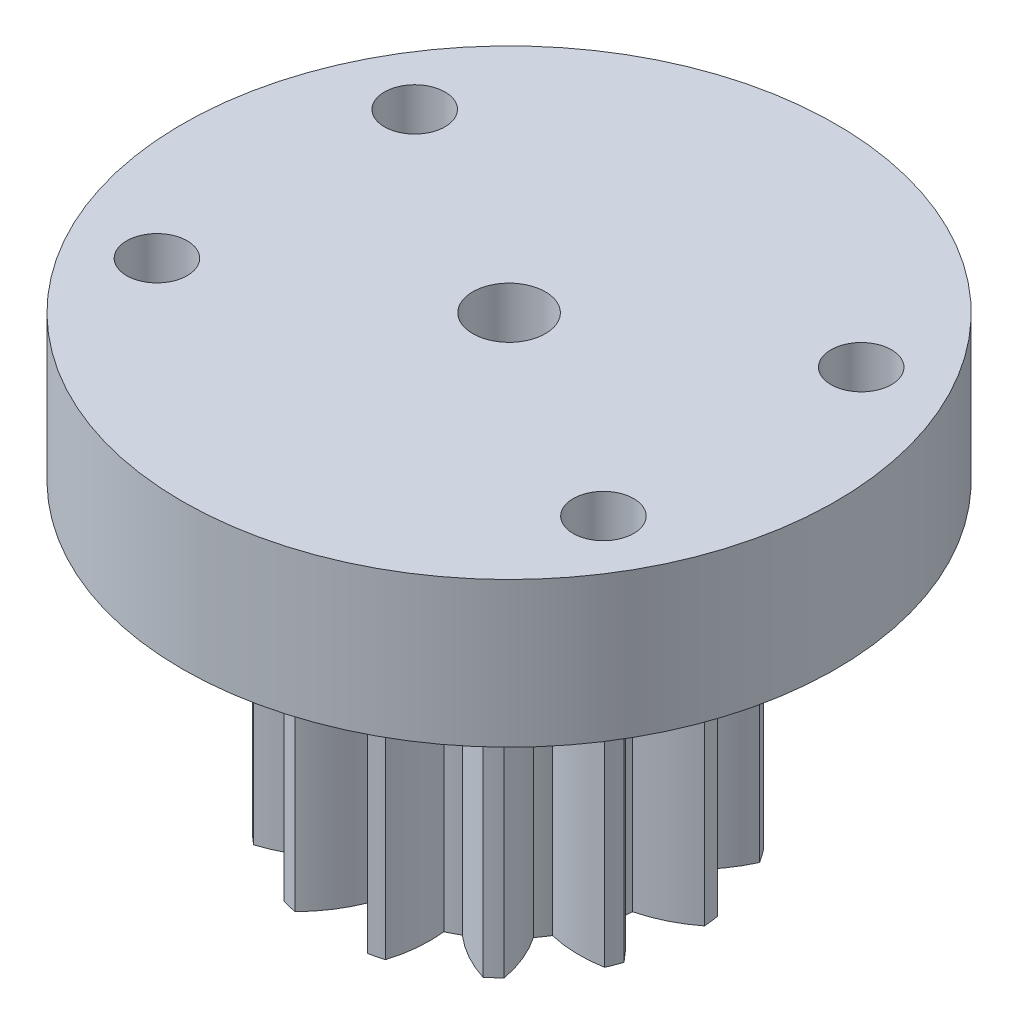
SolidWorks part; units mm, degrees
material "PLA"
ref_plane "Front Plane" through (0, 0, 0) normal (0, 0, 1) x (1, 0, 0)
ref_plane "Top Plane" through (0, 0, 0) normal (0, 1, 0) x (1, 0, 0)
ref_plane "Right Plane" through (0, 0, 0) normal (1, 0, 0) x (0, 0, -1)
sketch "Sketch1" plane through (0, 0, 0) normal (0, 1, 0) x (1, 0, 0)
  line L0 (0, 0) -> (0, 10.3828) construction
  arc A0 (0.31, 7.4936) -> (-0.31, 7.4936) centre (0, 0) ccw
  circle A1 centre (0, 0) radius 5.5
  arc A2 (-1.04, 5.4008) -> (-0.31, 7.4936) centre (4.3152, 4.7065) cw
  arc A3 (1.04, 5.4008) -> (0.31, 7.4936) centre (-4.3152, 4.7065) ccw
  arc A4 (1.589, 5.2655) -> (3.208, 6.7793) centre (6.0081, 2.1621) cw
  arc A5 (3.4307, 4.2988) -> (3.7569, 6.4912) centre (-1.6337, 6.1728) ccw
  arc A6 (3.7569, 6.4912) -> (3.208, 6.7793) centre (0, 0) ccw
  arc A7 (3.854, 3.9239) -> (5.991, 4.512) centre (6.3247, -0.8777) cw
  arc A8 (5.0355, 2.2121) -> (6.3432, 4.0017) centre (1.4221, 6.225) ccw
  arc A9 (6.3432, 4.0017) -> (5.991, 4.512) centre (0, 0) ccw
  arc A10 (5.236, 1.6834) -> (7.4016, 1.211) centre (5.1924, -3.7164) cw
  arc A11 (5.4868, -0.3814) -> (7.4763, 0.5955) centre (4.1521, 4.851) ccw
  arc A12 (7.4763, 0.5955) -> (7.4016, 1.211) centre (0, 0) ccw
  arc A13 (5.4186, -0.9427) -> (7.1166, -2.3674) centre (2.8705, -5.7037) cw
  arc A14 (4.681, -2.8876) -> (6.8967, -2.9471) centre (5.9309, 2.3658) ccw
  arc A15 (6.8967, -2.9471) -> (7.1166, -2.3674) centre (0, 0) ccw
  arc A16 (4.3598, -3.3529) -> (5.2012, -5.4035) centre (-0.1089, -6.3844) cw
  arc A17 (2.8029, -4.7322) -> (4.7371, -5.8146) centre (6.351, -0.6614) ccw
  arc A18 (4.7371, -5.8146) -> (5.2012, -5.4035) centre (0, 0) ccw
  arc A19 (2.3023, -4.995) -> (2.0943, -7.2017) centre (-3.0634, -5.6025) cw
  arc A20 (0.2827, -5.4927) -> (1.4923, -7.35) centre (5.3161, -3.5371) ccw
  arc A21 (1.4923, -7.35) -> (2.0943, -7.2017) centre (0, 0) ccw
  arc A22 (-0.2827, -5.4927) -> (-1.4923, -7.35) centre (-5.3161, -3.5371) cw
  arc A23 (-2.3023, -4.995) -> (-2.0943, -7.2017) centre (3.0634, -5.6025) ccw
  arc A24 (-2.0943, -7.2017) -> (-1.4923, -7.35) centre (0, 0) ccw
  arc A25 (-2.8029, -4.7322) -> (-4.7371, -5.8146) centre (-6.351, -0.6614) cw
  arc A26 (-4.3598, -3.3529) -> (-5.2012, -5.4035) centre (0.1089, -6.3844) ccw
  arc A27 (-5.2012, -5.4035) -> (-4.7371, -5.8146) centre (0, 0) ccw
  arc A28 (-4.681, -2.8876) -> (-6.8967, -2.9471) centre (-5.9309, 2.3658) cw
  arc A29 (-5.4186, -0.9427) -> (-7.1166, -2.3674) centre (-2.8705, -5.7037) ccw
  arc A30 (-7.1166, -2.3674) -> (-6.8967, -2.9471) centre (0, 0) ccw
  arc A31 (-5.4868, -0.3814) -> (-7.4763, 0.5955) centre (-4.1521, 4.851) cw
  arc A32 (-5.236, 1.6834) -> (-7.4016, 1.211) centre (-5.1924, -3.7164) ccw
  arc A33 (-7.4016, 1.211) -> (-7.4763, 0.5955) centre (0, 0) ccw
  arc A34 (-5.0355, 2.2121) -> (-6.3432, 4.0017) centre (-1.4221, 6.225) cw
  arc A35 (-3.854, 3.9239) -> (-5.991, 4.512) centre (-6.3247, -0.8777) ccw
  arc A36 (-5.991, 4.512) -> (-6.3432, 4.0017) centre (0, 0) ccw
  arc A37 (-3.4307, 4.2988) -> (-3.7569, 6.4912) centre (1.6337, 6.1728) cw
  arc A38 (-1.589, 5.2655) -> (-3.208, 6.7793) centre (-6.0081, 2.1621) ccw
  arc A39 (-3.208, 6.7793) -> (-3.7569, 6.4912) centre (0, 0) ccw
  point P73 (0, 0)
  point P86 (0, 0)
  dimension "D1" = 15
  dimension "D2" = 11
  dimension "D5" = 5.4
  dimension "D3" = 0.62
  dimension "D4" = 2.08
  dimension "D6" = 13
extrude "Boss-Extrude1" add sketch "Sketch1" along normal blind 12.5
sketch "Sketch2" plane through (0, 12.5, 0) normal (0, 1, 0) x (1, 0, 0)
  circle A0 centre (0, 0) radius 1.5
  dimension "D1" = 3
extrude "Cut-Extrude1" cut sketch "Sketch2" against normal through all
sketch "Esboço1" plane through (0, 12.5, 0) normal (0, 1, 0) x (1, 0, 0)
  line L0 (0, 9.9) -> (0, -9.9) construction
  circle A0 centre (0, 0) radius 10.65 construction
  circle A1 centre (0, 10.65) radius 0.75
  circle A2 centre (0, -10.65) radius 0.75
  circle A3 centre (10.65, 0) radius 0.75
  circle A4 centre (-10.65, 0) radius 0.75
  circle A5 centre (0, 0) radius 13.5
  circle A6 centre (0, 10.65) radius 1.25
  circle A10 centre (0, 0) radius 1.5 construction
  circle A11 centre (0, 0) radius 1.5
  circle A12 centre (9.2232, 5.325) radius 1.25
  circle A13 centre (9.2232, -5.325) radius 1.25
  circle A14 centre (0, -10.65) radius 1.25
  circle A15 centre (-9.2232, -5.325) radius 1.25
  circle A16 centre (-9.2232, 5.325) radius 1.25
  point P31 (0, 0)
  dimension "D1" = 1.5
  dimension "D3" = 27
  dimension "D4" = 2.5
  dimension "D2" = 19.8
  dimension "D5" = 6
extrude "Ressalto-extrusão1" add sketch "Esboço1" along normal blind 6 contours A5 | A16 | A15 | A13 | A12 | A11
